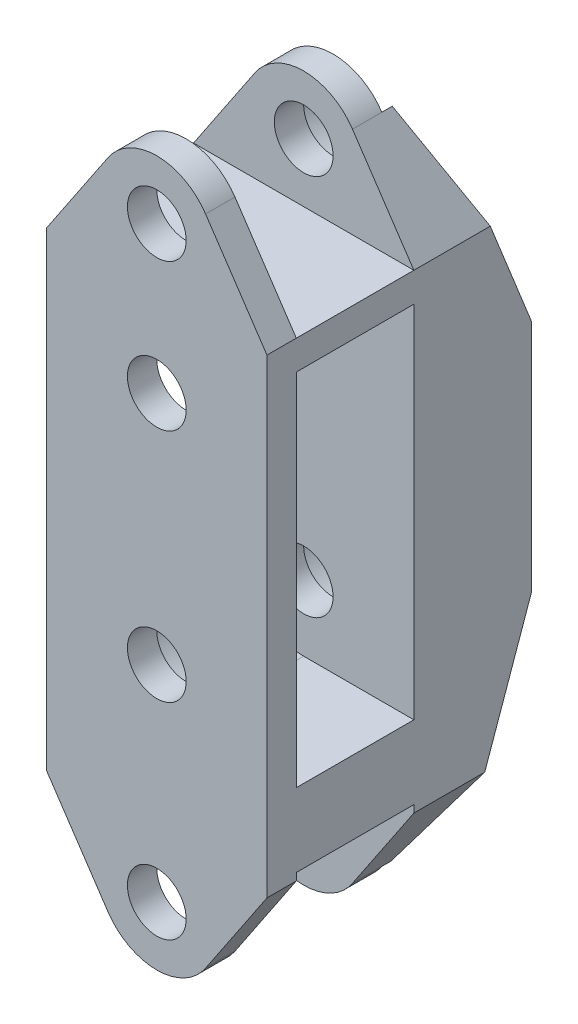
SolidWorks part; units mm, degrees
ref_plane "Front" through (0, 0, 0) normal (0, 0, 1) x (1, 0, 0)
ref_plane "Top" through (0, 0, 0) normal (0, 1, 0) x (1, 0, 0)
ref_plane "Right" through (0, 0, 0) normal (1, 0, 0) x (0, 0, -1)
sketch "Sketch1" plane through (0, 0, 0) normal (0, 0, 1) x (1, 0, 0)
  line L1 (-11.9063, -38.1) -> (11.9062, -38.1)
  line L2 (-11.9063, -38.1) -> (-11.9063, 38.1)
  line L3 (-11.9063, 38.1) -> (11.9062, 38.1)
  line L4 (11.9062, -38.1) -> (11.9062, 38.1)
  line L5 (-11.9063, -38.1) -> (11.9062, 38.1) construction
  line L6 (-11.9063, 38.1) -> (11.9062, -38.1) construction
  point P0 (0, 0)
  dimension "D1" = 76.2
  dimension "D2" = 23.8125
extrude "Boss-Extrude1" add sketch "Sketch1" along normal blind 28.575
sketch "Sketch2" plane through (0, 0, 28.575) normal (0, 0, 1) x (1, 0, 0)
  line L0 (0, 15.875) -> (0, 31.75) construction
  line L1 (0, -31.75) -> (0, -9.525) construction
  line L2 (11.9062, 38.1) -> (-11.9063, 38.1) construction
  line L3 (-11.9063, -38.1) -> (11.9062, -38.1) construction
  line L5 (11.9062, -38.1) -> (11.9062, 38.1) construction
  line L7 (0, 15.875) -> (0, 0) construction
  line L8 (11.9062, -25.4) -> (11.9062, -38.1)
  line L9 (0, 0) -> (0, -9.525) construction
  line L10 (11.9062, -38.1) -> (0, -38.1)
  line L12 (11.9062, -25.4) -> (5.2734, -35.2875)
  line L14 (-11.9062, -25.4) -> (-5.2734, -35.2875)
  line L15 (-11.9062, -25.4) -> (11.9062, -25.4) construction
  line L24 (5.2734, 35.2875) -> (11.9062, 25.4)
  line L27 (-5.2734, 35.2875) -> (-11.9062, 25.4)
  line L30 (-11.9062, 25.4) -> (11.9062, 25.4) construction
  line L31 (-11.9062, 25.4) -> (-11.9063, 38.1)
  line L42 (-11.9063, 38.1) -> (0, 38.1)
  line L44 (0, -38.1) -> (-11.9063, -38.1)
  line L45 (-11.9063, -38.1) -> (-11.9062, -25.4)
  line L48 (11.9062, 25.4) -> (11.9063, 38.1)
  line L49 (0, 38.1) -> (11.9063, 38.1)
  circle A0 centre (0, 31.75) radius 3.175
  circle A1 centre (0, 15.875) radius 3.175
  circle A2 centre (0, -9.525) radius 3.175
  circle A3 centre (0, -31.75) radius 3.175
  arc A4 (5.2734, 35.2875) -> (-5.2734, 35.2875) centre (0, 31.75) ccw construction
  arc A5 (-5.2734, -35.2875) -> (5.2734, -35.2875) centre (0, -31.75) ccw construction
  arc A6 (5.2734, 35.2875) -> (-5.2734, 35.2875) centre (0, 31.75) ccw
  arc A9 (-5.2734, -35.2875) -> (5.2734, -35.2875) centre (0, -31.75) ccw
  point P32 (0, -25.4)
  dimension "D1" = 12.7
  dimension "D4" = 6.35
  dimension "D3" = 6.35
  dimension "D2" = 15.875
  dimension "D5" = 22.225
extrude "Cut-Extrude1" cut sketch "Sketch2" against normal blind 31.75
sketch "Sketch11" plane through (0, 0, 0) normal (1, 0, 0) x (0, 0, -1)
  line L0 (0, 38.1) -> (-28.575, 38.1) construction
  line L1 (-25.4, 38.1) -> (-12.7, 38.1)
  line L2 (-25.4, 38.1) -> (-25.4, 25.4)
  line L3 (-25.4, 25.4) -> (-12.7, 25.4)
  line L4 (-12.7, 38.1) -> (-12.7, 25.4)
  line L5 (-25.4, 31.75) -> (-28.575, 31.75) construction
  line L6 (-28.575, 35.2875) -> (-28.575, 25.4) construction
  line L7 (-28.575, -38.1) -> (0, -38.1) construction
  line L8 (-25.4, 22.225) -> (-12.7, 22.225)
  line L9 (-25.4, 22.225) -> (-25.4, -38.1)
  line L10 (-25.4, -38.1) -> (-12.7, -38.1)
  line L11 (-12.7, 22.225) -> (-12.7, -38.1)
  line L12 (-19.05, 22.225) -> (-19.05, 25.4) construction
  line L13 (0, 14.2875) -> (0, -11.1125) construction
  line L14 (0, -25.4) -> (0, 25.4) construction
  line L15 (0, 14.2875) -> (-9.525, 38.1)
  line L16 (-9.525, 38.1) -> (0, 38.1)
  line L17 (0, 38.1) -> (0, 14.2875)
  line L18 (0, -11.1125) -> (-9.525, -38.1)
  line L19 (-9.525, -38.1) -> (0, -38.1)
  line L20 (0, -38.1) -> (0, -11.1125)
  line L21 (-12.7, -38.1) -> (-9.525, -38.1) construction
  line L22 (-12.7, 38.1) -> (-9.525, 38.1) construction
  dimension "D1" = 3.175
  dimension "D2" = 12.7
  dimension "D3" = 25.4
  dimension "D4" = 23.8125
extrude "Cut-Extrude7" cut sketch "Sketch11" against normal through all both and the other way through all
sketch "Sketch12" plane through (0, 0, 25.4) normal (0, 0, -1) x (-1, 0, 0)
  line L0 (0, -24.6063) -> (-11.9062, -24.6063)
  line L1 (-11.9062, -25.4) -> (-11.9062, 25.4) construction
  line L2 (0, -16.6687) -> (-11.9062, -16.6687)
  line L3 (7.1437, -9.525) -> (11.9063, -9.525)
  line L4 (11.9063, 25.4) -> (11.9063, -25.4) construction
  line L5 (11.9063, -9.525) -> (11.9063, -25.4)
  line L6 (11.9063, -25.4) -> (7.0966, -32.5697)
  line L7 (11.9063, -25.4) -> (5.2734, -35.2875) construction
  line L8 (-11.9062, -24.6063) -> (-11.9062, -16.6687)
  circle A0 centre (0, -31.75) radius 6.35 construction
  arc A1 (-5.2734, -35.2875) -> (5.2734, -35.2875) centre (0, -31.75) ccw construction
  circle A2 centre (0, -9.525) radius 6.35 construction
  arc A3 (7.0966, -32.5697) -> (0, -24.6063) centre (0, -31.75) ccw
  arc A4 (0, -16.6687) -> (7.1437, -9.525) centre (0, -9.525) ccw
  circle A5 centre (0, -9.525) radius 7.1437 construction
  circle A6 centre (0, -31.75) radius 7.1437 construction
  dimension "D1" = 0.7937
  dimension "D2" = 0.7937
extrude "Boss-Extrude3" add sketch "Sketch12" along normal up to surface (12.7 mm away) contours L5 L6 A3 L0 L8 L2 A4 L3 up to face at (0, -6.35, 12.7)
sketch "Sketch13" plane through (0, 0, 12.7) normal (0, 0, 1) x (1, 0, 0)
  circle A0 centre (0, 31.75) radius 6.35
  arc A1 (5.2734, 35.2875) -> (-5.2734, 35.2875) centre (0, 31.75) ccw construction
  circle A2 centre (0, 15.875) radius 6.35
  circle A3 centre (0, -9.525) radius 6.35
  circle A4 centre (0, -31.75) radius 6.35
  arc A5 (-5.2734, -35.2875) -> (5.2734, -35.2875) centre (0, -31.75) ccw construction
extrude "Cut-Extrude8" cut sketch "Sketch13" against normal through all from offset 3.175
